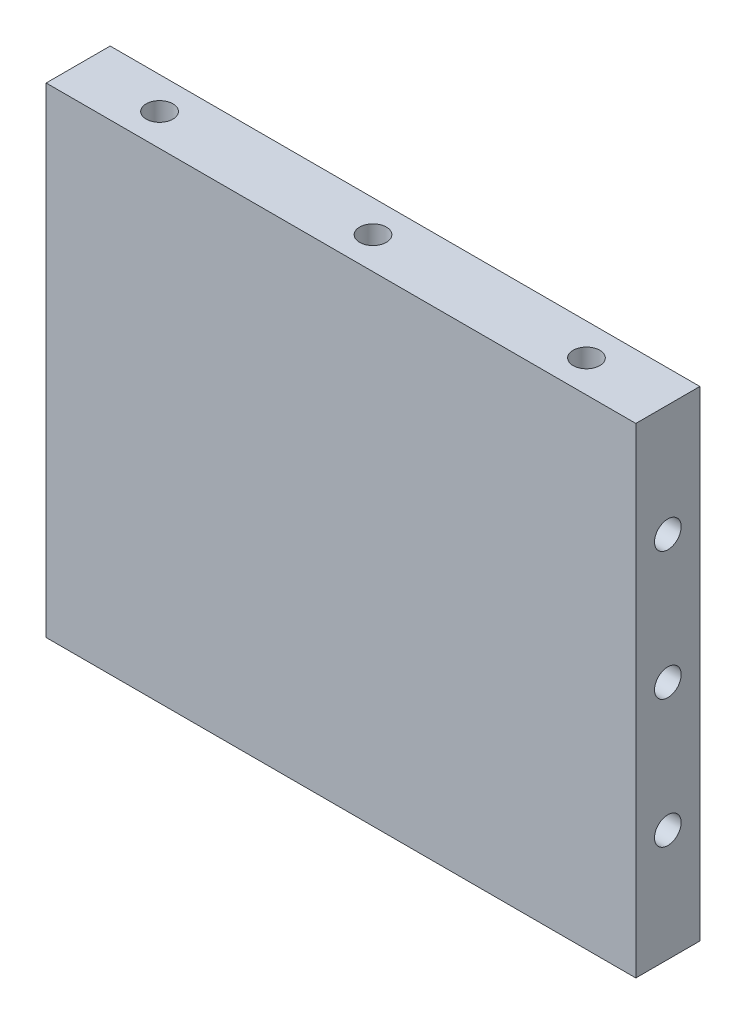
SolidWorks part; units mm, degrees
material "6063-T5"
ref_plane "前视基准面" through (0, 0, 0) normal (0, 0, 1) x (1, 0, 0)
ref_plane "上视基准面" through (0, 0, 0) normal (0, 1, 0) x (1, 0, 0)
ref_plane "右视基准面" through (0, 0, 0) normal (1, 0, 0) x (0, 0, -1)
other "Configuration Table"
sketch "草图1" plane through (0, 0, 0) normal (0, 0, 1) x (1, 0, 0)
  line L1 (-27.625, -22.5) -> (27.625, -22.5)
  line L2 (-27.625, -22.5) -> (-27.625, 22.5)
  line L3 (-27.625, 22.5) -> (27.625, 22.5)
  line L4 (27.625, -22.5) -> (27.625, 22.5)
  line L5 (-27.625, -22.5) -> (27.625, 22.5) construction
  line L6 (-27.625, 22.5) -> (27.625, -22.5) construction
  point P0 (0, 0)
  dimension "D1" = 55.25
  dimension "D2" = 45
extrude "凸台-拉伸1" add sketch "草图1" along normal blind 6
sketch "草图2" plane through (0, 22.5, 0) normal (0, 1, 0) x (1, 0, 0)
  line L0 (0, 0) -> (0, 50000) construction
  line L1 (26.125, -3) -> (50026.125, -3) construction
  line L2 (27.625, -6) -> (27.625, 0) construction
  circle A0 centre (0, -3) radius 2.525
  circle A1 centre (-20, -3) radius 2.525
  circle A2 centre (20, -3) radius 2.525
  point P7 (27.625, -3)
  dimension "D1" = 5.05
  dimension "D2" = 20
sketch "草图3" plane through (0, 22.5, 0) normal (0, 1, 0) x (1, 0, 0)
  point P0 (-20, -3)
  point P3 (0, -3)
  point P6 (20, -3)
hole_wizard "M3 螺纹孔1" positions "草图3" profile "草图4" tap size "M3" standard "GB" end condition through all
sketch "草图4" plane through (-20, 22.5, 3) normal (1, 0, 0) x (0, 0, 1)
  line L0 (0, 0) -> (0, 45)
  line L1 (0, 45) -> (1.25, 45)
  line L2 (1.25, 45) -> (1.25, 0)
  line L5 (1.25, 0) -> (0, 0)
  line L11 (0, -6.35) -> (0, 107.95) construction
  dimension "通孔螺纹孔钻头直径" = 2.5
  dimension "通孔螺纹孔钻头深度" = 45
cosmetic thread "孔螺蚊线1" parameters "D2"=3
cosmetic thread "孔螺蚊线2" parameters "D2"=3
cosmetic thread "孔螺蚊线3" parameters "D2"=3
sketch "草图5" plane through (-27.625, 0, 0) normal (-1, 0, 0) x (0, 0, 1)
  line L0 (3, 17.5) -> (3, 50017.5) construction
  line L1 (5.525, 22.5) -> (0.475, 22.5) construction
  line L2 (0, 0) -> (50000, 0) construction
  circle A0 centre (3, 12) radius 1.1739 construction
  circle A1 centre (3, -12) radius 1.1739 construction
  point P4 (3, 22.5)
  dimension "D1" = 2.3477
  dimension "D2" = 12
sketch "草图6" plane through (-27.625, 0, 0) normal (-1, 0, 0) x (0, 0, 1)
  line L0 (3, -199982.5) -> (3, 250017.5) construction
  line L1 (-200000, 0) -> (250000, 0) construction
  point P0 (3, 12)
  point P3 (3, -12)
  point P6 (3, 0)
hole_wizard "M3 螺纹孔2" positions "草图6" profile "草图7" tap size "M3" standard "GB" end condition through all
sketch "草图7" plane through (-27.625, 12, 3) normal (0, 1, 0) x (0, 0, 1)
  line L0 (0, 0) -> (0, 55.25)
  line L1 (0, 55.25) -> (1.25, 55.25)
  line L2 (1.25, 55.25) -> (1.25, 0)
  line L5 (1.25, 0) -> (0, 0)
  line L11 (0, -6.35) -> (0, 107.95) construction
  dimension "通孔螺纹孔钻头直径" = 2.5
  dimension "通孔螺纹孔钻头深度" = 55.25
cosmetic thread "孔螺蚊线4" parameters "D2"=3
cosmetic thread "孔螺蚊线5" parameters "D2"=3
cosmetic thread "孔螺蚊线6" parameters "D2"=3
